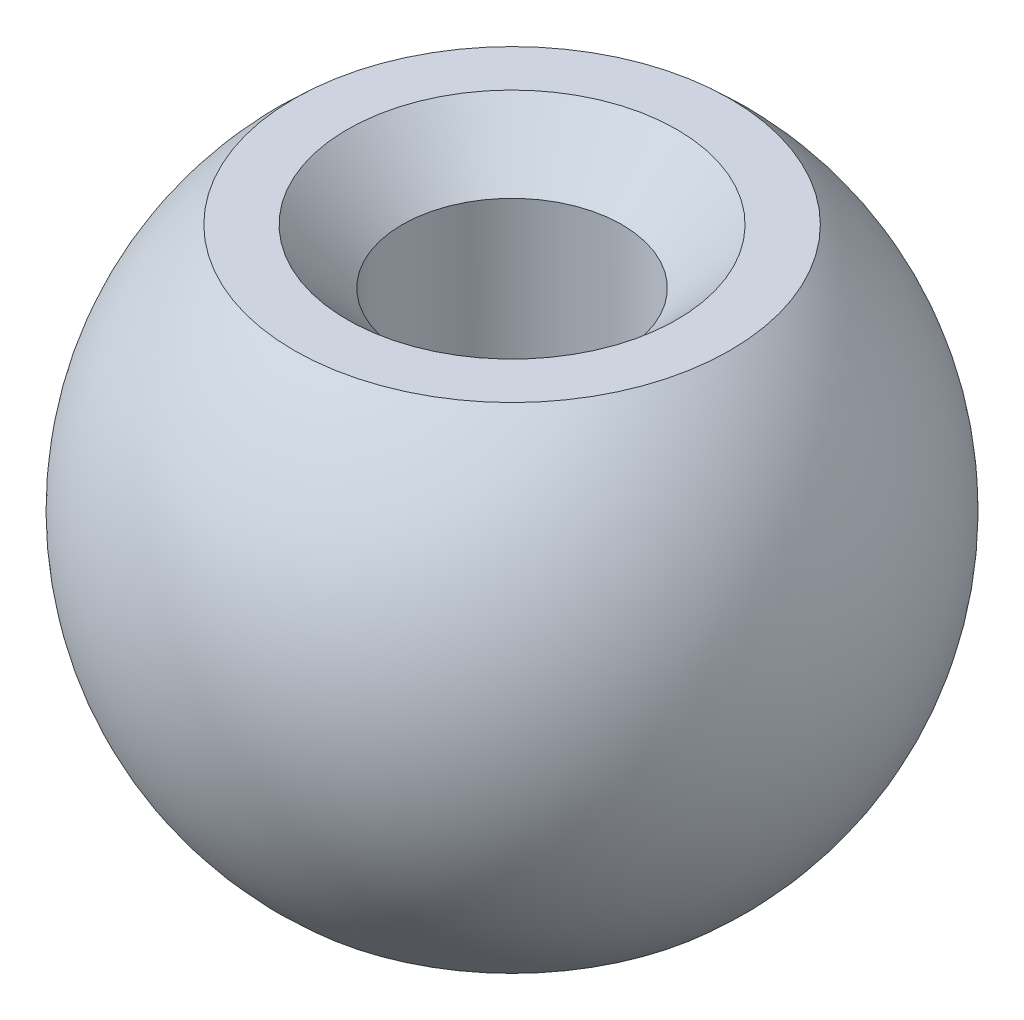
SolidWorks part; units mm, degrees
ref_plane "Front Plane" through (0, 0, 0) normal (0, 0, 1) x (1, 0, 0)
ref_plane "Top Plane" through (0, 0, 0) normal (0, 1, 0) x (1, 0, 0)
ref_plane "Right Plane" through (0, 0, 0) normal (1, 0, 0) x (0, 0, -1)
sketch "Sketch3" plane through (0, 0, 0) normal (0, 0, 1) x (1, 0, 0)
  line L0 (6, 0) -> (8.2854, 0) construction
  line L1 (2, -4.5) -> (3.9686, -4.5)
  line L2 (0, 5.5345) -> (0, -5.7608) construction
  line L7 (2, 4.5) -> (2, -4.5)
  line L8 (2, 4.5) -> (3.9686, 4.5)
  line L9 (4.8, -3.6) -> (5.1439, -3.8579) construction
  arc A2 (3.9686, -4.5) -> (3.9686, 4.5) centre (0, 0) ccw
  point P0 (0, 0)
  dimension "D1" = 4.5
revolve "Revolve1" add sketch "Sketch3" angle 360 about L2
chamfer "Chamfer1" distance 1 angle 45 1 edges at (0, 4.5, 2)
